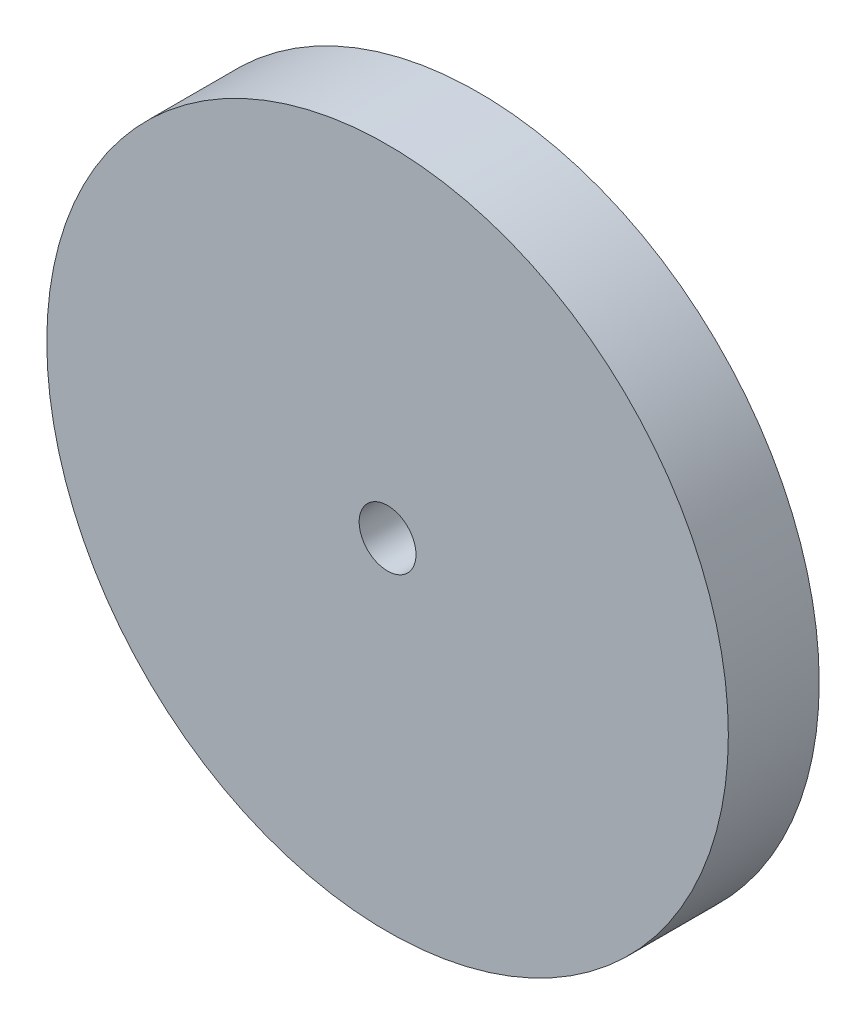
SolidWorks part; units mm, degrees
material "Acrílico (Impacto medio-alto)"
ref_plane "Alzado" through (0, 0, 0) normal (0, 0, 1) x (1, 0, 0)
ref_plane "Planta" through (0, 0, 0) normal (0, 1, 0) x (1, 0, 0)
ref_plane "Vista lateral" through (0, 0, 0) normal (1, 0, 0) x (0, 0, -1)
sketch "Croquis1" plane through (0, 0, 0) normal (0, 0, 1) x (1, 0, 0)
  circle A0 centre (0, 0) radius 15
  circle A1 centre (0, 0) radius 1.25
  dimension "D1" = 30
  dimension "D2" = 2.5
extrude "Saliente-Extruir1" add sketch "Croquis1" along normal mid plane 4
